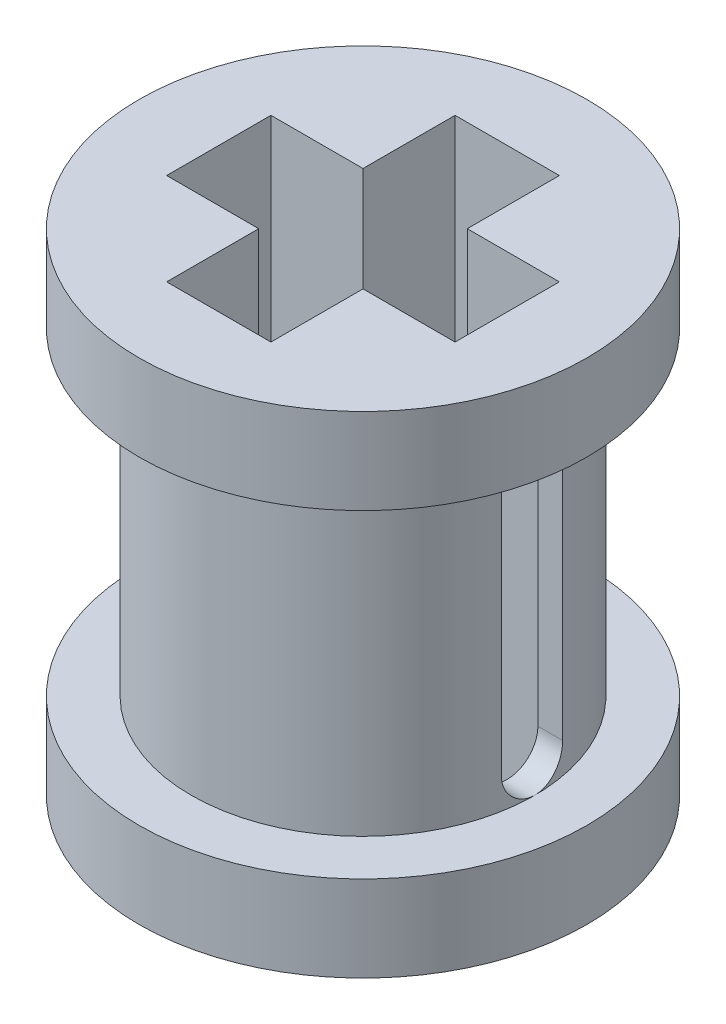
SolidWorks part; units mm, degrees
ref_plane "Front Plane" through (0, 0, 0) normal (0, 0, 1) x (1, 0, 0)
ref_plane "Top Plane" through (0, 0, 0) normal (0, 1, 0) x (1, 0, 0)
ref_plane "Right Plane" through (0, 0, 0) normal (1, 0, 0) x (0, 0, -1)
sketch "Sketch2" plane through (0, 0, 0) normal (0, 1, 0) x (1, 0, 0)
  circle A0 centre (0, 0) radius 3.65
  dimension "D1" = 7.3
extrude "Boss-Extrude1" add sketch "Sketch2" along normal blind 1.4
sketch "Sketch3" plane through (0, 1.4, 0) normal (0, 1, 0) x (1, 0, 0)
  circle A0 centre (0, 0) radius 2.8
  dimension "D1" = 5.6
extrude "Boss-Extrude2" add sketch "Sketch3" along normal blind 5.2
sketch "Sketch4" plane through (0, 6.6, 0) normal (0, 1, 0) x (1, 0, 0)
  circle A0 centre (0, 0) radius 3.65
  dimension "D1" = 7.3
extrude "Boss-Extrude3" add sketch "Sketch4" along normal blind 1.4
sketch "Sketch5" plane through (0, 8, 0) normal (0, 1, 0) x (1, 0, 0)
  line L0 (-0.85, 0.85) -> (-0.85, 2.3511)
  line L1 (-2.3511, 0.85) -> (-0.85, 0.85)
  line L2 (-2.3511, 0.85) -> (-2.3511, -0.85)
  line L3 (-2.3511, -0.85) -> (-0.85, -0.85)
  line L4 (2.3511, 0.85) -> (2.3511, -0.85)
  line L5 (0.85, 0.85) -> (0.85, 2.3511)
  line L6 (0.85, 0.85) -> (2.3511, 0.85)
  line L7 (0.85, -2.3511) -> (-0.85, -2.3511)
  line L8 (0.85, -2.3511) -> (0.85, -0.85)
  line L9 (0.85, 2.3511) -> (-0.85, 2.3511)
  line L10 (-0.85, -2.3511) -> (-0.85, -0.85)
  line L11 (0.85, -0.85) -> (2.3511, -0.85)
  circle A0 centre (0, 0) radius 2.5
  dimension "D1" = 5
  dimension "D2" = 1.7
  dimension "D3" = 1.7
extrude "Cut-Extrude1" cut sketch "Sketch5" against normal through all contours L8 L11 L4 L6 L5 L9 L0 L1 L2 L3 L10 L7
ref_plane "Plane1" through (10, 0, 0) normal (1, 0, 0) x (0, 0, -1)
sketch "Sketch6" plane through (10, 0, 0) normal (1, 0, 0) x (0, 0, -1)
  line L0 (0, 0) -> (0, 8) construction
  line L1 (0.85, 8) -> (-0.85, 8) construction
  line L2 (0, 6.0987) -> (0, 1.9013) construction
  line L3 (0.5, 6.0987) -> (0.5, 1.9013)
  line L4 (-0.5, 6.0987) -> (-0.5, 1.9013)
  arc A0 (0.5, 6.0987) -> (-0.5, 6.0987) centre (0, 6.0987) ccw
  arc A1 (-0.5, 1.9013) -> (0.5, 1.9013) centre (0, 1.9013) ccw
  point P7 (0, 4)
extrude "Cut-Extrude2" cut sketch "Sketch6" against normal through all
